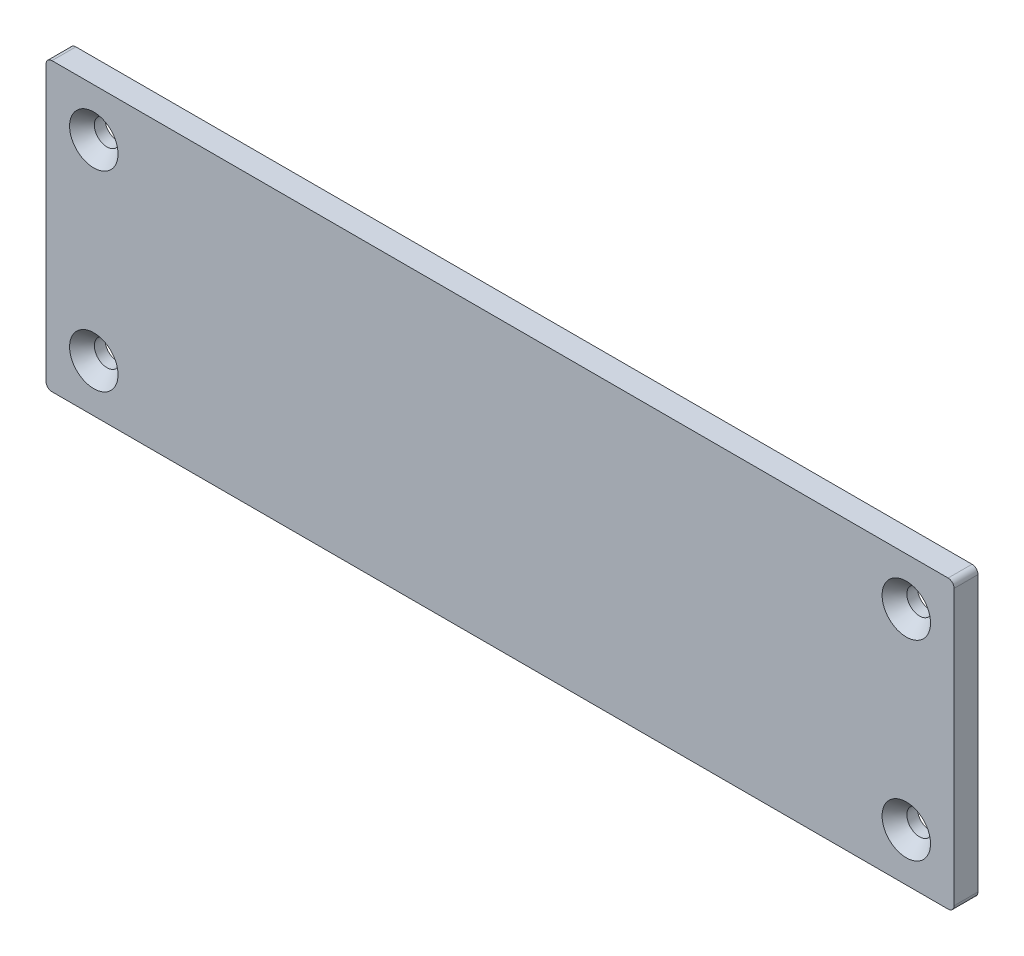
SolidWorks part; units mm, degrees
material "PE High Density Film"
ref_plane "Front Plane" through (0, 0, 0) normal (0, 0, 1) x (1, 0, 0)
ref_plane "Top Plane" through (0, 0, 0) normal (0, 1, 0) x (1, 0, 0)
ref_plane "Right Plane" through (0, 0, 0) normal (1, 0, 0) x (0, 0, -1)
sketch "Sketch1" plane through (0, 0, 0) normal (0, 0, 1) x (1, 0, 0)
  line L1 (-120.65, 38.1) -> (120.65, 38.1)
  line L2 (-120.65, 38.1) -> (-120.65, -38.1)
  line L3 (-120.65, -38.1) -> (120.65, -38.1)
  line L4 (120.65, 38.1) -> (120.65, -38.1)
  line L5 (-120.65, 38.1) -> (120.65, -38.1) construction
  line L6 (-120.65, -38.1) -> (120.65, 38.1) construction
  point P0 (0, 0)
  dimension "D1" = 76.2
  dimension "D2" = 241.3
extrude "Boss-Extrude1" add sketch "Sketch1" along normal blind 6.35
sketch "Sketch2" plane through (0, 0, 6.35) normal (0, 0, 1) x (1, 0, 0)
  line L0 (120.65, 38.1) -> (-120.65, 38.1) construction
  line L1 (107.95, 25.4) -> (-107.95, 25.4)
  line L2 (107.95, 25.4) -> (107.95, -25.4)
  line L3 (107.95, -25.4) -> (-107.95, -25.4)
  line L4 (-107.95, 25.4) -> (-107.95, -25.4)
  line L5 (107.95, 25.4) -> (-107.95, -25.4) construction
  line L6 (107.95, -25.4) -> (-107.95, 25.4) construction
  line L7 (-120.65, 38.1) -> (-120.65, -38.1) construction
  line L8 (-107.95, -25.4) -> (107.95, -25.4)
  line L10 (-107.95, 25.4) -> (107.95, 25.4)
  point P0 (0, 0)
  dimension "D1" = 12.7
  dimension "D2" = 12.7
  dimension "D3" = 50.8
  dimension "D4" = 50.8
hole_wizard "CSK for 1/4 Flat Head Machine Screw (100)1" positions "Sketch3" profile "Sketch4" countersink size "1/4" standard "ANSI Inch" end condition up to next
sketch "Sketch3" plane through (0, 0, 6.35) normal (0, 0, 1) x (1, 0, 0)
  point P9 (107.95, 25.4)
  point P12 (107.95, -25.4)
  point P18 (-107.95, 25.4)
  point P21 (-107.95, -25.4)
  point P24 (0, 0)
  point P25 (0, 0)
  point P26 (0, 0)
  point P27 (0, 0)
  point P28 (0, 0)
sketch "Sketch4" plane through (107.95, 25.4, 6.35) normal (1, 0, 0) x (0, -1, 0)
  line L0 (0, 0) -> (0, 6.35)
  line L1 (0, 6.35) -> (3.3782, 6.35)
  line L2 (3.3782, 6.35) -> (3.3782, 3.5209)
  line L3 (3.3782, 3.5209) -> (6.4389, 0)
  line L5 (6.4389, 0) -> (0, 0)
  line L6 (-3.3782, 3.5209) -> (-6.4389, 0) construction
  line L11 (0, -6.35) -> (0, 107.95) construction
  dimension "Thru Hole Dia." = 6.7564
  dimension "Thru Hole Depth" = 6.35
  dimension "Near C'Sink Dia." = 12.8778
  dimension "Near C'Sink Angle" = 82
fillet "Fillet1" radius 1.5875 4 edges at (120.65, 38.1, 3.175) (120.65, -38.1, 3.175) (-120.65, 38.1, 3.175) (-120.65, -38.1, 3.175)
